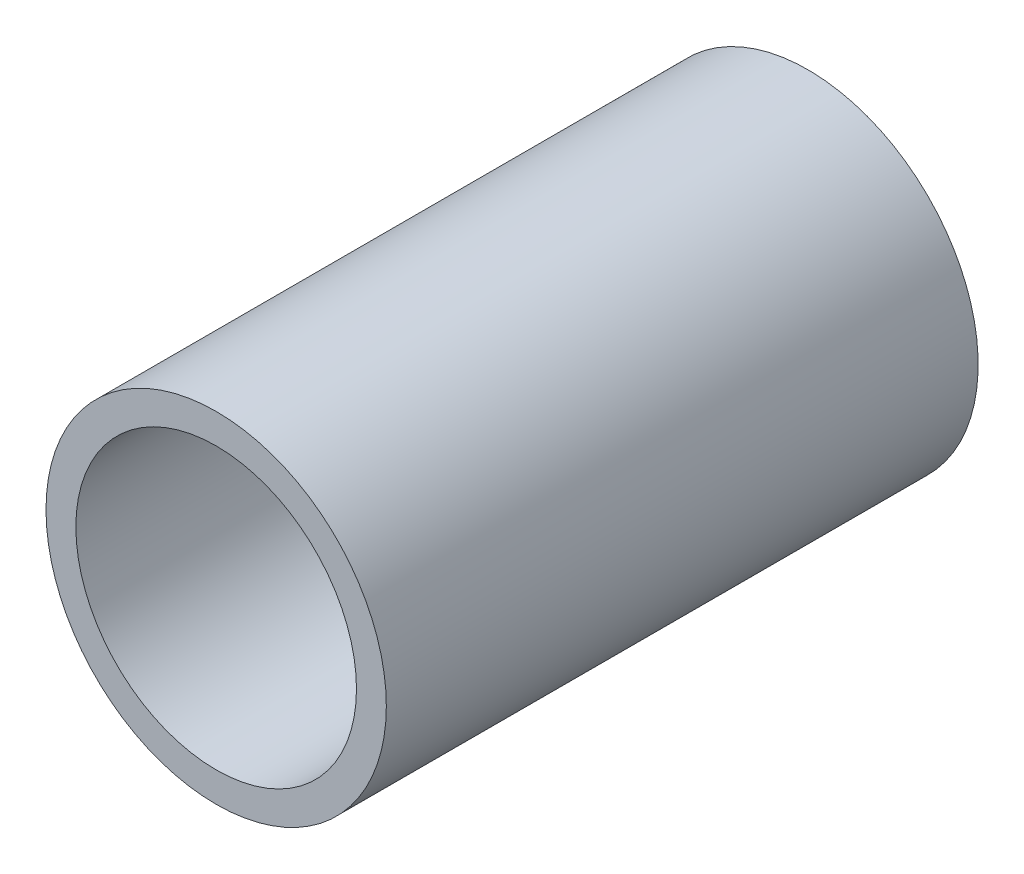
SolidWorks part; units mm, degrees
ref_plane "Front Plane" through (0, 0, 0) normal (0, 0, 1) x (1, 0, 0)
ref_plane "Top Plane" through (0, 0, 0) normal (0, 1, 0) x (1, 0, 0)
ref_plane "Right Plane" through (0, 0, 0) normal (1, 0, 0) x (0, 0, -1)
sketch "Sketch1" plane through (0, 0, 0) normal (0, 0, 1) x (1, 0, 0)
  circle A0 centre (0, 0) radius 5.7
  dimension "D1" = 11.4
extrude "Boss-Extrude1" add sketch "Sketch1" along normal blind 31 contours A0
sketch "Sketch2" plane through (0, 0, 31) normal (0, 0, 1) x (1, 0, 0)
  circle A0 centre (0, 0) radius 4.7
  dimension "D1" = 9.4
extrude "Cut-Extrude1" cut sketch "Sketch2" against normal blind 33.302
ref_plane "Plane1" through (0, 0, 0) normal (0, 0, -1) x (-1, 0, 0)
ref_plane "Plane2" through (0, 0, 11.176) normal (0, 0, -1) x (-1, 0, 0)
ref_plane "Plane3" through (0, 0, 31) normal (0, 0, 1) x (1, 0, 0)
ref_plane "Plane4" through (0, 0, 19.824) normal (0, 0, 1) x (1, 0, 0)
sketch "Sketch5" plane through (0, 0, 19.824) normal (0, 0, 1) x (1, 0, 0)
  circle A1 centre (0, 0) radius 4.7
  circle A2 centre (0, 0) radius 4.192
  dimension "D2" = 8.384
  dimension "D1" = 0.508
extrude "Boss-Extrude3" add sketch "Sketch5" against normal blind 0.635
sketch "Sketch8" plane through (0, 0, 0) normal (0, 0, -1) x (-1, 0, 0)
  circle A0 centre (0, 0) radius 5.7 construction
  circle A1 centre (0, 0) radius 5.7
  circle A2 centre (0, 0) radius 4.7 construction
  circle A3 centre (0, 0) radius 4.7
extrude "Cut-Extrude2" cut sketch "Sketch8" against normal blind 11.176
